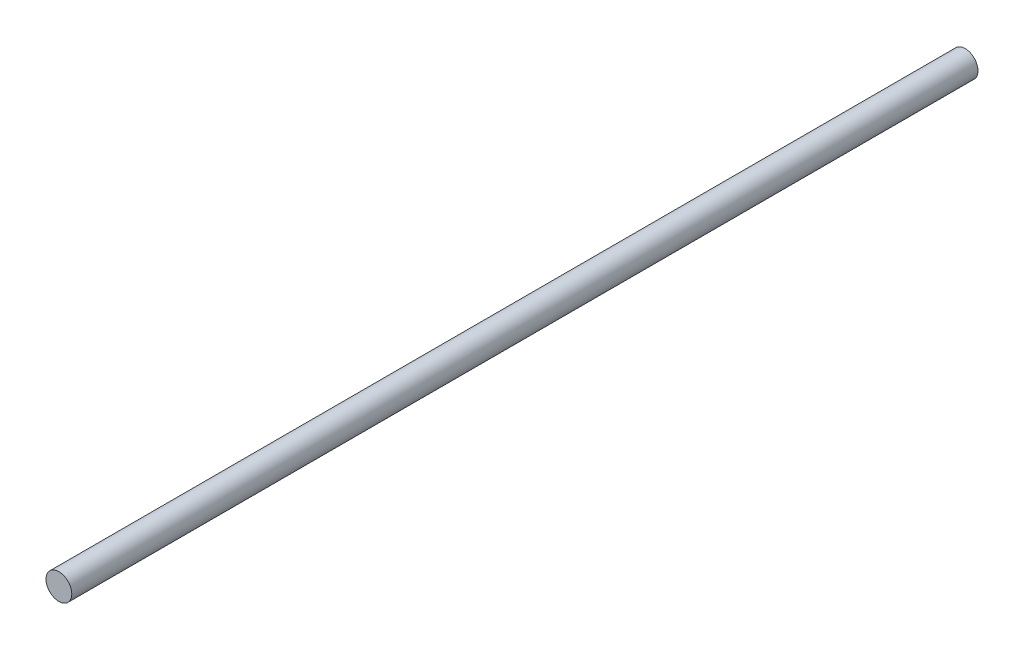
SolidWorks part; units mm, degrees
ref_plane "Front Plane" through (0, 0, 0) normal (0, 0, 1) x (1, 0, 0)
ref_plane "Top Plane" through (0, 0, 0) normal (0, 1, 0) x (1, 0, 0)
ref_plane "Right Plane" through (0, 0, 0) normal (1, 0, 0) x (0, 0, -1)
sketch "Sketch1" plane through (0, 0, 0) normal (0, 0, 1) x (1, 0, 0)
  circle A0 centre (0, 0) radius 3.175
  dimension "D1" = 6.35
extrude "Boss-Extrude1" add sketch "Sketch1" along normal blind 223
